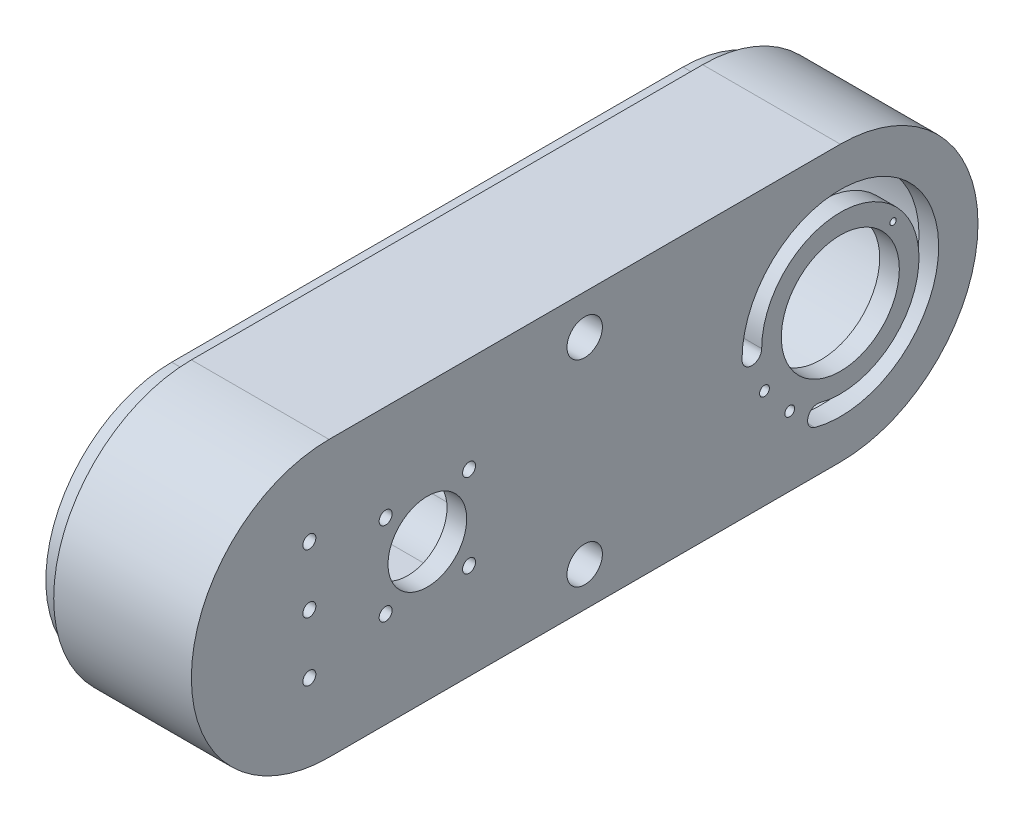
SolidWorks part; units mm, degrees
ref_plane "정면" through (0, 0, 0) normal (0, 0, 1) x (1, 0, 0)
ref_plane "윗면" through (0, 0, 0) normal (0, 1, 0) x (1, 0, 0)
ref_plane "우측면" through (0, 0, 0) normal (1, 0, 0) x (0, 0, -1)
sketch "스케치1" plane through (0, 0, 0) normal (1, 0, 0) x (0, 0, -1)
  line L1 (-48.263, 12.7105) -> (81.737, 12.7105)
  line L3 (-48.263, -57.2895) -> (81.737, -57.2895)
  arc A4 (81.737, -57.2895) -> (81.737, 12.7105) centre (81.737, -22.2895) ccw
  arc A5 (-48.263, 12.7105) -> (-48.263, -57.2895) centre (-48.263, -22.2895) ccw
  point P8 (116.737, 12.7105)
  point P11 (-83.263, -57.2895)
  point P14 (-83.263, 12.7105)
  dimension "D1" = 70
  dimension "D2" = 200
extrude "보스-돌출1" add sketch "스케치1" against normal blind 35
sketch "스케치3" plane through (-35, 0, 0) normal (-1, 0, 0) x (0, 0, 1)
  line L13 (48.263, 7.7105) -> (-81.737, 7.7105)
  line L15 (-81.737, -52.2895) -> (48.263, -52.2895)
  line L17 (48.263, 7.7105) -> (-81.737, 7.7105)
  line L19 (-81.737, -52.2895) -> (48.263, -52.2895)
  arc A2 (48.263, -52.2895) -> (48.263, 7.7105) centre (48.263, -22.2895) ccw
  arc A3 (-81.737, 7.7105) -> (-81.737, -52.2895) centre (-81.737, -22.2895) ccw
  arc A4 (48.263, -52.2895) -> (48.263, 7.7105) centre (48.263, -22.2895) ccw
  arc A8 (-81.737, 7.7105) -> (-81.737, -52.2895) centre (-81.737, -22.2895) ccw
  dimension "D1" = 5
extrude "컷-돌출2" cut sketch "스케치3" against normal blind 30
sketch "스케치4" plane through (0, 0, 0) normal (1, 0, 0) x (0, 0, -1)
  line L0 (-1082.4298, 12.7105) -> (48917.5702, 12.7105) construction
  line L2 (-1069.2501, -57.2895) -> (48930.7499, -57.2895) construction
  line L4 (-116.737, -1000.8602) -> (-116.737, 48999.1398) construction
  line L6 (83.263, -1020.218) -> (83.263, 48979.782) construction
  line L8 (-48.263, 12.7105) -> (81.737, 12.7105) construction
sketch "스케치2" plane through (0, 0, 0) normal (1, 0, 0) x (0, 0, -1)
  line L0 (-1038.5373, 12.7105) -> (48961.4627, 12.7105) construction
  line L1 (-48.263, 12.7105) -> (81.737, 12.7105) construction
  line L2 (-1020.2333, -57.3029) -> (48979.7667, -57.3029) construction
  line L3 (-23.263, -22.3029) -> (-23.263, 49977.6971) construction
  line L4 (116.737, -1002.7262) -> (116.737, 48997.2738) construction
  line L5 (-23.263, -22.3029) -> (35332.076, -35377.6419) construction
  line L6 (-83.263, -1008.4848) -> (-83.263, 48991.5152) construction
  line L7 (-23.263, -22.3029) -> (35332.076, 35333.0362) construction
  line L8 (-943.505, -22.3029) -> (49056.495, -22.3029) construction
  line L9 (-53.263, 12.6971) -> (-8.263, 12.6971) construction
  line L10 (-53.263, 12.6971) -> (-53.263, -57.3029) construction
  line L11 (-53.263, -57.3029) -> (-8.263, -57.3029) construction
  line L12 (-8.263, 12.6971) -> (-8.263, -57.3029) construction
  circle A0 centre (-53.263, -22.3029) radius 2 construction
  circle A1 centre (-23.263, -22.3029) radius 15
  circle A2 centre (-12.6564, -32.9095) radius 2 construction
  circle A3 centre (-33.8696, -32.9095) radius 2 construction
  circle A4 centre (-12.6564, -11.6963) radius 2 construction
  circle A6 centre (-53.263, -7.3029) radius 2 construction
  circle A7 centre (-53.263, -37.3029) radius 2 construction
  circle A9 centre (-23.263, -22.3029) radius 10
  circle A10 centre (81.737, -22.3029) radius 15
  circle A11 centre (-33.8696, -11.6963) radius 2 construction
  arc A13 (81.737, -57.2895) -> (81.737, 12.7105) centre (81.737, -22.2895) ccw construction
  point P14 (0, 0)
  point P16 (-53.263, -22.3029)
  point P33 (116.737, -22.2895)
  point P46 (0, 0)
  point P48 (0, 0)
  dimension "D1" = 30
  dimension "D2" = 30
  dimension "D3" = 4
  dimension "D4" = 45
  dimension "D7" = 35
  dimension "D8" = 30
  dimension "D9" = 35
  dimension "D5" = 15
  dimension "D6" = 15
extrude "컷-돌출1" cut sketch "스케치2" against normal through all both and the other way through all contours A4 | A11 | A2 | A6 | A0 | A7 | A3 | A9 | A10
sketch "스케치6" plane through (-35, 0, 0) normal (-1, 0, 0) x (0, 0, 1)
  line L8 (-81.737, -54.2895) -> (48.263, -54.2895)
  line L9 (48.263, 9.7105) -> (-81.737, 9.7105)
  line L12 (-81.737, -52.2895) -> (48.263, -52.2895)
  line L13 (48.263, 7.7105) -> (-81.737, 7.7105)
  line L14 (-81.737, -52.2895) -> (48.263, -52.2895)
  line L15 (48.263, 7.7105) -> (-81.737, 7.7105)
  arc A10 (-81.737, 9.7105) -> (-81.737, -54.2895) centre (-81.737, -22.2895) ccw
  arc A11 (48.263, -54.2895) -> (48.263, 9.7105) centre (48.263, -22.2895) ccw
  arc A12 (48.263, -52.2895) -> (48.263, 7.7105) centre (48.263, -22.2895) ccw
  arc A13 (-81.737, 7.7105) -> (-81.737, -52.2895) centre (-81.737, -22.2895) ccw
  arc A14 (48.263, -52.2895) -> (48.263, 7.7105) centre (48.263, -22.2895) ccw
  arc A15 (-81.737, 7.7105) -> (-81.737, -52.2895) centre (-81.737, -22.2895) ccw
  dimension "D1" = 0
  dimension "D2" = 2
extrude "보스-돌출2" add sketch "스케치6" along normal blind 5
sketch "스케치8" plane through (0, 0, 0) normal (1, 0, 0) x (0, 0, -1)
  line L0 (81.737, -1072.2762) -> (81.737, -47.2895) construction
  line L1 (81.737, -42.2895) -> (81.737, 49977.6971) construction
  line L2 (81.737, -22.2895) -> (-12859.2153, -48318.5808) construction
  line L3 (80.5213, -22.2895) -> (-49919.4787, -22.2895) construction
  line L5 (81.737, -22.2895) -> (50081.737, -22.2895) construction
  arc A0 (76.5606, -41.608) -> (61.737, -22.2895) centre (81.737, -22.2895) ccw
  arc A1 (75.2665, -46.4377) -> (56.737, -22.2895) centre (81.737, -22.2895) ccw
  arc A2 (56.737, -22.2895) -> (61.737, -22.2895) centre (59.237, -22.2895) ccw
  arc A3 (76.5606, -41.608) -> (75.2665, -46.4377) centre (75.9136, -44.0229) ccw
  dimension "D1" = 40
  dimension "D2" = 50
  dimension "D5" = 5
  dimension "D6" = 5
  dimension "D3" = 15
  dimension "D7" = 22.5
  dimension "D8" = 22.5
extrude "컷-돌출4" cut sketch "스케치8" against normal up to next
sketch "스케치9" plane through (-5, 0, 0) normal (-1, 0, 0) x (0, 0, 1)
  line L0 (-81.737, -22.3029) -> (-81.737, -44.3748) construction
  line L1 (-88.6083, -22.3029) -> (49911.3917, -22.3029) construction
  line L2 (-81.737, -22.3029) -> (38220.4754, -32161.6752) construction
  line L3 (-81.737, -22.2895) -> (32057.6435, 38279.9326) construction
  circle A0 centre (-62.4427, -31.9657) radius 1.5
  circle A2 centre (-95.1428, -11.0541) radius 1
  circle A3 centre (-68.8706, -39.6261) radius 1.5
  point P13 (-81.737, -22.3029)
  dimension "D1" = 2
  dimension "D2" = 3
  dimension "D4" = 3
  dimension "D3" = 17.5
  dimension "D5" = 5
  dimension "D6" = 5
  dimension "D7" = 40
  dimension "D8" = 21
  dimension "D9" = 21
sketch "스케치11" plane through (-5, 0, 0) normal (-1, 0, 0) x (0, 0, 1)
  line L0 (-16.737, 5.801) -> (-16.737, -49994.199) construction
  line L2 (-42.9301, 12.7105) -> (-50042.9301, 12.7105) construction
  line L3 (-81.737, -22.2895) -> (-81.737, 49977.7105) construction
  line L4 (-76.1627, -57.2895) -> (-50076.1627, -57.2895) construction
  circle A0 centre (-16.737, -47.2895) radius 6
  circle A1 centre (-16.737, 2.7105) radius 6
  dimension "D2" = 12
  dimension "D3" = 12
  dimension "D1" = 65
  dimension "D4" = 10
  dimension "D5" = 10
extrude "보스-돌출4" add sketch "스케치11" along normal blind 35
sketch "스케치12" plane through (0, 0, 0) normal (1, 0, 0) x (0, 0, -1)
  line L0 (-28.0855, 12.7105) -> (-50028.0855, 12.7105) construction
  line L2 (-33.8211, -57.2895) -> (-50033.8211, -57.2895) construction
  line L4 (16.737, 12.7105) -> (16.737, 50012.7105) construction
  line L5 (81.737, 12.7105) -> (-48.263, 12.7105) construction
  circle A0 centre (16.737, -47.2895) radius 2.25
  circle A1 centre (16.737, 2.7105) radius 2.25
  point P8 (16.737, 12.7105)
  point P13 (0, 0)
  dimension "D1" = 4.5
  dimension "D2" = 4.5
  dimension "D3" = 10
  dimension "D4" = 10
fillet "필렛1" radius 10 4 edges at (-22.5, -52.2895, -20.0536) (-22.5, -52.2895, -13.4204) (-22.5, 7.7105, -13.4204) (-22.5, 7.7105, -20.0536)
hole_wizard "M3 나사 구멍1" positions "스케치14" profile "스케치15" tap size "M3" standard "ISO" end condition through all
sketch "스케치14" plane through (-5, 0, 0) normal (-1, 0, 0) x (0, 0, 1)
  point P0 (-62.4427, -31.9657)
  point P3 (-68.8706, -39.6261)
sketch "스케치15" plane through (-5, -31.9657, -62.4427) normal (0, 1, 0) x (0, 0, 1)
  line L0 (0, 0) -> (0, 5)
  line L1 (0, 5) -> (1.25, 5)
  line L2 (1.25, 5) -> (1.25, 0)
  line L5 (1.25, 0) -> (0, 0)
  line L11 (0, -6.35) -> (0, 107.95) construction
  dimension "관통 탭 드릴 지름" = 2.5
  dimension "관통 탭 드릴 깊이" = 5
cosmetic thread "구멍 나사산1" parameters "D2"=3
cosmetic thread "구멍 나사산2" parameters "D2"=3
hole_wizard "M2 나사 구멍1" positions "스케치16" profile "스케치17" tap size "M2" standard "ISO" end condition through all
sketch "스케치16" plane through (-5, 0, 0) normal (-1, 0, 0) x (0, 0, 1)
  point P0 (-95.1428, -11.0541)
sketch "스케치17" plane through (-5, -11.0541, -95.1428) normal (0, 1, 0) x (0, 0, 1)
  line L0 (0, 0) -> (0, 5)
  line L1 (0, 5) -> (0.8, 5)
  line L2 (0.8, 5) -> (0.8, 0)
  line L5 (0.8, 0) -> (0, 0)
  line L11 (0, -6.35) -> (0, 107.95) construction
  dimension "관통 탭 드릴 지름" = 1.6
  dimension "관통 탭 드릴 깊이" = 5
cosmetic thread "구멍 나사산3" parameters "D2"=2
hole_wizard "M4 나사 구멍1" positions "스케치18" profile "스케치19" tap size "M4" standard "ISO" end condition through all
sketch "스케치18" plane through (0, 0, 0) normal (1, 0, 0) x (0, 0, -1)
  point P0 (-53.263, -7.3029)
  point P3 (-53.263, -22.3029)
  point P6 (-53.263, -37.3029)
  point P9 (-33.8696, -32.9095)
  point P12 (-33.8696, -11.6963)
  point P15 (-12.6564, -11.6963)
  point P18 (-12.6564, -32.9095)
sketch "스케치19" plane through (0, -7.3029, 53.263) normal (0, 1, 0) x (0, 0, -1)
  line L0 (0, 0) -> (0, 40)
  line L1 (0, 40) -> (1.65, 40)
  line L2 (1.65, 40) -> (1.65, 0)
  line L5 (1.65, 0) -> (0, 0)
  line L11 (0, -6.35) -> (0, 107.95) construction
  dimension "관통 탭 드릴 지름" = 3.3
  dimension "관통 탭 드릴 깊이" = 40
cosmetic thread "구멍 나사산4" parameters "D2"=4
cosmetic thread "구멍 나사산5" parameters "D2"=4
cosmetic thread "구멍 나사산6" parameters "D2"=4
cosmetic thread "구멍 나사산7" parameters "D2"=4
cosmetic thread "구멍 나사산8" parameters "D2"=4
cosmetic thread "구멍 나사산9" parameters "D2"=4
cosmetic thread "구멍 나사산10" parameters "D2"=4
hole_wizard "M4 남비 머리 나사용 카운터보어2" positions "스케치22" profile "스케치23" counterbore size "M4" standard "ISO"
sketch "스케치22" plane through (0, 0, 0) normal (1, 0, 0) x (0, 0, -1)
  point P0 (16.737, 2.7105)
  point P3 (16.737, -47.2895)
sketch "스케치23" plane through (0, 2.7105, -16.737) normal (0, 1, 0) x (0, 0, -1)
  line L0 (0, 0) -> (0, 41.3519)
  line L1 (0, 41.3519) -> (2.25, 40)
  line L2 (2.25, 40) -> (2.25, 33.1)
  line L3 (2.25, 33.1) -> (4.5, 33.1)
  line L4 (4.5, 33.1) -> (4.5, 0)
  line L5 (4.5, 0) -> (0, 0)
  line L10 (0, 41.3519) -> (-2.25, 40) construction
  line L11 (0, -6.35) -> (0, 107.95) construction
  dimension "구멍 지름" = 4.5
  dimension "구멍 깊이" = 40
  dimension "카운터보어 지름" = 9
  dimension "카운터보어 깊이" = 33.1
  dimension "드릴 각도" = 118
